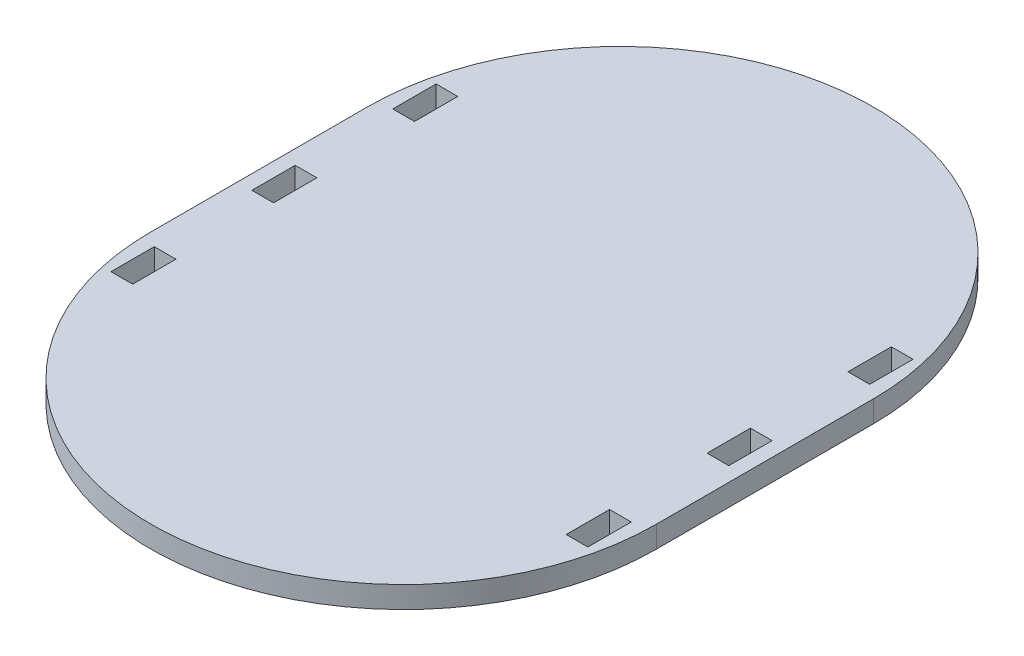
SolidWorks part; units mm, degrees
ref_plane "Front Plane" through (0, 0, 0) normal (0, 0, 1) x (1, 0, 0)
ref_plane "Top Plane" through (0, 0, 0) normal (0, 1, 0) x (1, 0, 0)
ref_plane "Right Plane" through (0, 0, 0) normal (1, 0, 0) x (0, 0, -1)
sketch "Sketch1" plane through (0, 0, 0) normal (0, 1, 0) x (1, 0, 0)
  line L0 (0, 0) -> (0, 76.2) construction
  line L1 (-88.9, 0) -> (-88.9, 76.2)
  line L2 (88.9, 0) -> (88.9, 76.2)
  arc A0 (-88.9, 0) -> (88.9, 0) centre (0, 0) ccw
  arc A1 (88.9, 76.2) -> (-88.9, 76.2) centre (0, 76.2) ccw
  point P3 (0, 38.1)
  dimension "D2" = 88.9
  dimension "D1" = 76.2
extrude "Boss-Extrude1" add sketch "Sketch1" along normal blind 7.62 contours A1 L1 A0 L2
sketch "Sketch5" plane through (0, 7.62, 0) normal (0, 1, 0) x (1, 0, 0)
  line L0 (-88.9, 38.1) -> (88.9, 38.1) construction
  line L1 (-88.9, 0) -> (-88.9, 76.2) construction
  line L2 (88.9, 0) -> (88.9, 76.2) construction
  line L3 (0, 165.1) -> (0, -88.9) construction
  line L4 (-83.82, 95.25) -> (-83.82, -19.05) construction
  line L5 (83.82, -3.81) -> (76.2, -3.81)
  line L6 (-83.82, -19.05) -> (-76.2, -19.05)
  line L7 (-83.82, -19.05) -> (-83.82, -3.81)
  line L8 (-83.82, -3.81) -> (-76.2, -3.81)
  line L9 (-76.2, -19.05) -> (-76.2, -3.81)
  line L10 (-83.82, 95.25) -> (-76.2, 95.25)
  line L11 (-83.82, 95.25) -> (-83.82, 80.01)
  line L12 (-83.82, 80.01) -> (-76.2, 80.01)
  line L13 (-76.2, 95.25) -> (-76.2, 80.01)
  line L14 (76.2, -19.05) -> (76.2, -3.81)
  line L15 (83.82, -19.05) -> (76.2, -19.05)
  line L16 (83.82, -19.05) -> (83.82, -3.81)
  line L17 (83.82, 80.01) -> (76.2, 80.01)
  line L18 (76.2, 95.25) -> (76.2, 80.01)
  line L19 (83.82, 95.25) -> (76.2, 95.25)
  line L20 (83.82, 95.25) -> (83.82, 80.01)
  line L21 (83.82, 30.48) -> (76.2, 30.48)
  line L22 (-83.82, 45.72) -> (-76.2, 45.72)
  line L23 (-83.82, 45.72) -> (-83.82, 30.48)
  line L24 (-83.82, 30.48) -> (-76.2, 30.48)
  line L25 (-76.2, 45.72) -> (-76.2, 30.48)
  line L26 (76.2, 45.72) -> (76.2, 30.48)
  line L27 (83.82, 45.72) -> (76.2, 45.72)
  line L28 (83.82, 45.72) -> (83.82, 30.48)
  arc A0 (88.9, 76.2) -> (-88.9, 76.2) centre (0, 76.2) ccw construction
  arc A1 (-88.9, 0) -> (88.9, 0) centre (0, 0) ccw construction
  point P16 (-83.82, 38.1)
  point P35 (-76.2, 38.1)
  dimension "D1" = 114.3
  dimension "D2" = 0
  dimension "D3" = 5.08
  dimension "D4" = 15.24
  dimension "D5" = 7.62
  dimension "D6" = 7.62
  dimension "D7" = 15.24
  dimension "D8" = 15.24
  dimension "D9" = 7.62
  dimension "D10" = 0
extrude "Cut-Extrude5" cut sketch "Sketch5" against normal through all
equation "\"D1@Boss-Extrude1\"=\"MDF\""
equation "\"MDF\" = 0.3in"
equation "\"D5@Sketch5\"=\"MDF\""
equation "\"D9@Sketch5\"=\"MDF\""
